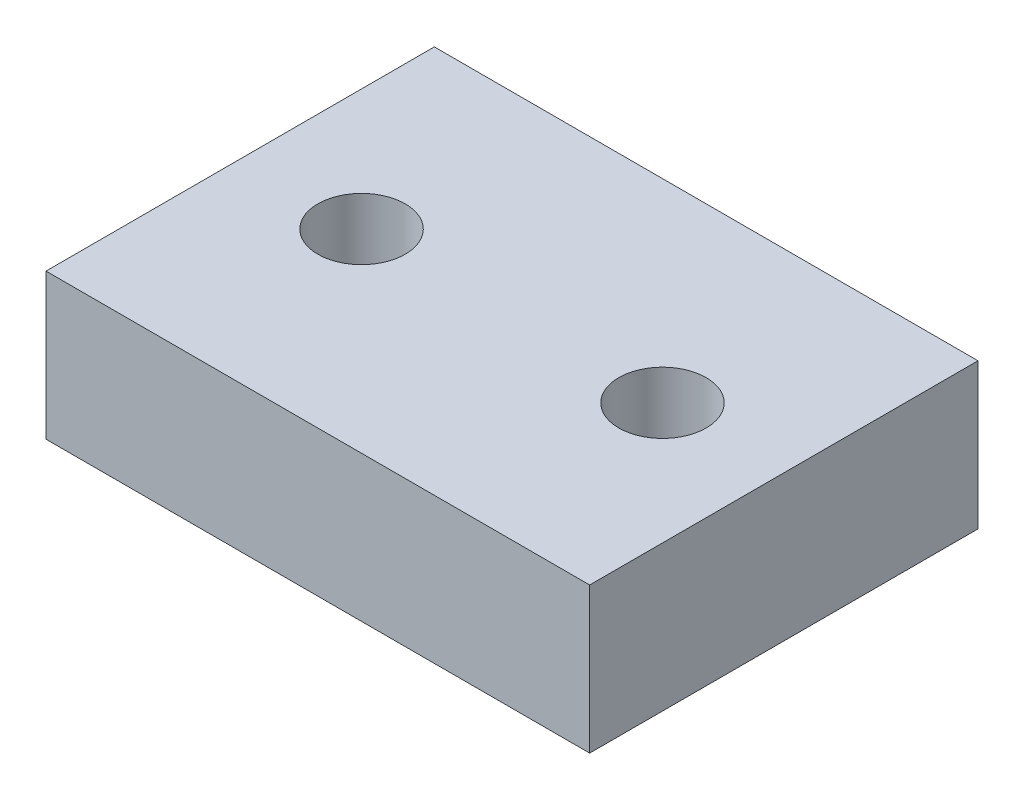
SolidWorks part; units mm, degrees
ref_plane "Front Plane" through (0, 0, 0) normal (0, 0, 1) x (1, 0, 0)
ref_plane "Top Plane" through (0, 0, 0) normal (0, 1, 0) x (1, 0, 0)
ref_plane "Right Plane" through (0, 0, 0) normal (1, 0, 0) x (0, 0, -1)
sketch "Sketch1" plane through (0, 0, 0) normal (0, 1, 0) x (1, 0, 0)
  line L0 (-10, 0) -> (10, 0) construction
  line L1 (14, -10) -> (-14, -10)
  line L2 (14, -10) -> (14, 10)
  line L3 (14, 10) -> (-14, 10)
  line L4 (-14, -10) -> (-14, 10)
  line L5 (14, -10) -> (-14, 10) construction
  line L6 (14, 10) -> (-14, -10) construction
  line L7 (-5.5, 0) -> (5.5, 0) construction
  circle A0 centre (-7.75, 0) radius 2.25
  circle A1 centre (7.75, 0) radius 2.25
  point P0 (0, 0)
  dimension "D1" = 20
  dimension "D2" = 28
  dimension "D3" = 20
  dimension "D4" = 11
extrude "Boss-Extrude1" add sketch "Sketch1" along normal mid plane 7.5
equation "\"m3 hole\"= 3.2"
equation "\"m4 hole\"= 4.2"
equation "\"m5 hole\"= 5.2"
equation "\"m6 hole\"= 6.2"
equation "\"m8 hole\"= 8.2"
equation "\"m3 tapped\"= 2.5"
equation "\"m4 tapped\"= 3.3"
equation "\"m5 tapped\"= 4.2"
equation "\"m6 tapped\"= 5"
equation "\"m8 tapped\"= 6.8"
